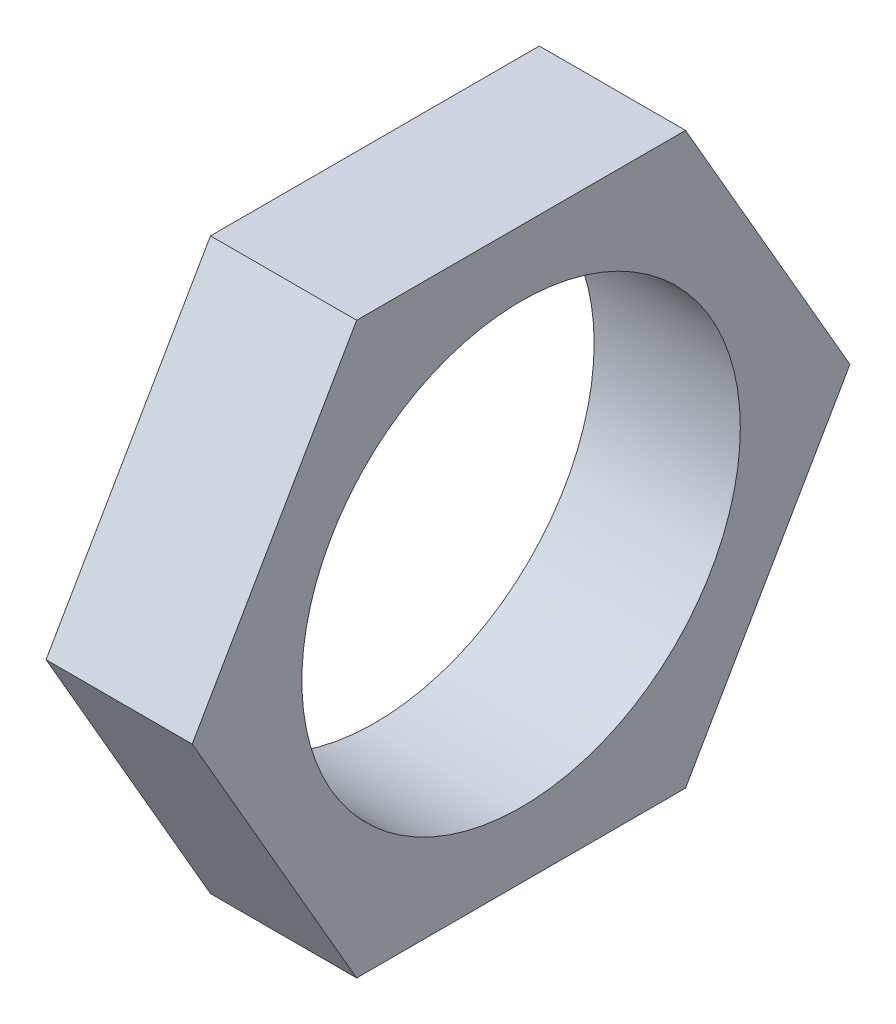
SolidWorks part; units mm, degrees
ref_plane "Front Plane" through (0, 0, 0) normal (0, 0, 1) x (1, 0, 0)
ref_plane "Top Plane" through (0, 0, 0) normal (0, 1, 0) x (1, 0, 0)
ref_plane "Right Plane" through (0, 0, 0) normal (1, 0, 0) x (0, 0, -1)
sketch "Sketch1" plane through (0, 0, 0) normal (1, 0, 0) x (0, 0, -1)
  line L1 (45, 0) -> (22.5, 38.9711)
  line L2 (22.5, 38.9711) -> (-22.5, 38.9711)
  line L3 (-22.5, 38.9711) -> (-45, 0)
  line L4 (-45, 0) -> (-22.5, -38.9711)
  line L5 (-22.5, -38.9711) -> (22.5, -38.9711)
  line L6 (22.5, -38.9711) -> (45, 0)
  circle A0 centre (0, 0) radius 38.9711 construction
  circle A1 centre (0, 0) radius 30
  dimension "D2" = 60
  dimension "D1" = 90
extrude "Boss-Extrude1" add sketch "Sketch1" along normal blind 20
